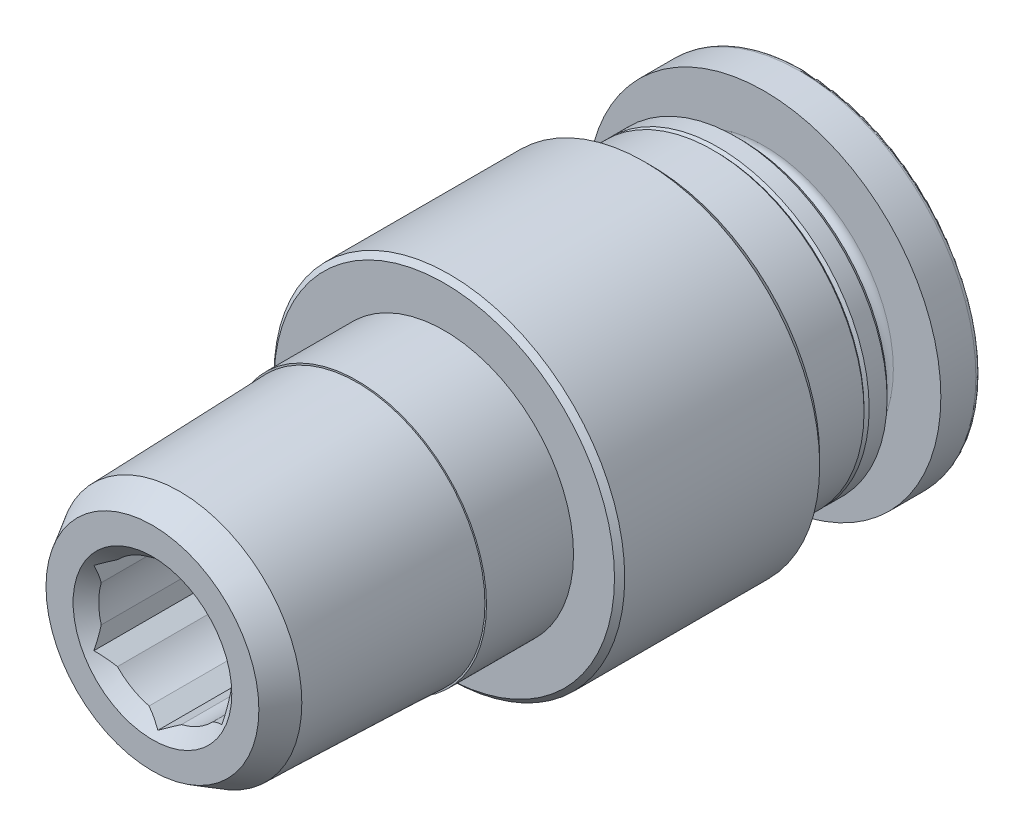
SolidWorks part; units mm, degrees
ref_plane "Front Plane" through (0, 0, 0) normal (0, 0, 1) x (1, 0, 0)
ref_plane "Top Plane" through (0, 0, 0) normal (0, 1, 0) x (1, 0, 0)
ref_plane "Right Plane" through (0, 0, 0) normal (1, 0, 0) x (0, 0, -1)
ref_plane "Plane1" through (0, 0, 0) normal (1, 0, 0) x (0, 0, -1)
sketch "Sketch1" plane through (0, 0, 0) normal (1, 0, 0) x (0, 0, -1)
  line L0 (0, 0) -> (0, 6.85)
  line L1 (0, 6.85) -> (11.2172, 6.85)
  line L2 (11.2172, 6.85) -> (11.5, 6.5672)
  line L3 (11.5, 6.5672) -> (11.5, 5.9)
  line L4 (11.5, 5.9) -> (13.9, 5.9)
  line L5 (13.9, 5.9) -> (14, 5.8)
  line L6 (14, 5.8) -> (14.1, 5.9)
  line L7 (14.1, 5.9) -> (14.8, 5.9)
  line L8 (14.8, 5.9) -> (15, 5.7)
  line L9 (15, 5.7) -> (15, 4.669)
  line L10 (15, 4.669) -> (15.525, 4.669)
  line L11 (15.9, 5.044) -> (15.9, 6.9)
  line L12 (15.9, 6.9) -> (17.2683, 6.9)
  line L13 (17.4652, 6.7347) -> (17.9, 4.269)
  line L14 (17.9, 4.269) -> (17.9, 0)
  line L15 (17.9, 0) -> (0, 0)
  line L16 (17.9, 0) -> (0, 0) construction
  arc A0 (15.525, 4.669) -> (15.9, 5.044) centre (15.525, 5.044) ccw
  arc A1 (17.2683, 6.9) -> (17.4652, 6.7347) centre (17.2683, 6.7) cw
revolve "Revolve1" add sketch "Sketch1" angle 360 about L16
ref_plane "Plane2" through (0, 0, 0) normal (1, 0, 0) x (0, 0, -1)
sketch "Sketch2" plane through (0, 0, 0) normal (1, 0, 0) x (0, 0, -1)
  line L0 (-8, 0) -> (-8, 4.1581)
  line L1 (-8, 4.1581) -> (-6.9362, 4.7723)
  line L2 (-6.9362, 4.7723) -> (0, 4.9889)
  line L3 (0, 4.9889) -> (0, 0)
  line L4 (0, 0) -> (-8, 0)
  line L5 (0, 0) -> (-8, 0) construction
revolve "Revolve2" add sketch "Sketch2" angle 360 about L5
ref_plane "Plane3" through (0, 0, 0) normal (1, 0, 0) x (0, 0, -1)
sketch "Sketch3" plane through (0, 0, 0) normal (1, 0, 0) x (0, 0, -1)
  line L0 (0, 6.85) -> (0, 5.05)
  line L1 (0, 5.05) -> (3.4, 5.05)
  line L2 (3.4, 5.05) -> (3.4, 6.65)
  line L3 (3.4, 6.65) -> (3.6, 6.85)
  line L4 (3.6, 6.85) -> (0, 6.85)
  line L5 (50, 0) -> (-50, 0) construction
revolve "Cut-Revolve1" cut sketch "Sketch3" angle 360 about L5
ref_plane "Plane4" through (0, 0, 0) normal (1, 0, 0) x (0, 0, -1)
sketch "Sketch4" plane through (0, 0, 0) normal (1, 0, 0) x (0, 0, -1)
  line L0 (-8, 0) -> (-8, 3.1)
  line L1 (-8, 3.1) -> (-7.5, 2.6)
  line L2 (-7.5, 2.6) -> (-0.3, 2.6)
  line L3 (-0.3, 2.6) -> (-0.3, 3.969)
  line L4 (-0.3, 3.969) -> (17.6, 3.969)
  line L5 (17.9, 4.269) -> (17.9, 0)
  line L6 (17.9, 0) -> (-8, 0)
  line L7 (17.9, 0) -> (-8, 0) construction
  arc A0 (17.6, 3.969) -> (17.9, 4.269) centre (17.6, 4.269) ccw
revolve "Cut-Revolve2" cut sketch "Sketch4" angle 360 about L7
ref_plane "Plane5" through (0, 0, 0.3) normal (0, 0, 1) x (1, 0, 0)
sketch "Sketch5" plane through (0, 0, 0.3) normal (0, 0, 1) x (1, 0, 0)
  line L0 (-2.5, -1.4434) -> (0, -2.8868)
  line L1 (0, -2.8868) -> (2.5, -1.4434)
  line L2 (2.5, -1.4434) -> (2.5, 1.4434)
  line L3 (2.5, 1.4434) -> (0, 2.8868)
  line L4 (0, 2.8868) -> (-2.5, 1.4434)
  line L5 (-2.5, 1.4434) -> (-2.5, -1.4434)
extrude "Cut-Extrude1" cut sketch "Sketch5" along normal blind 7.7
